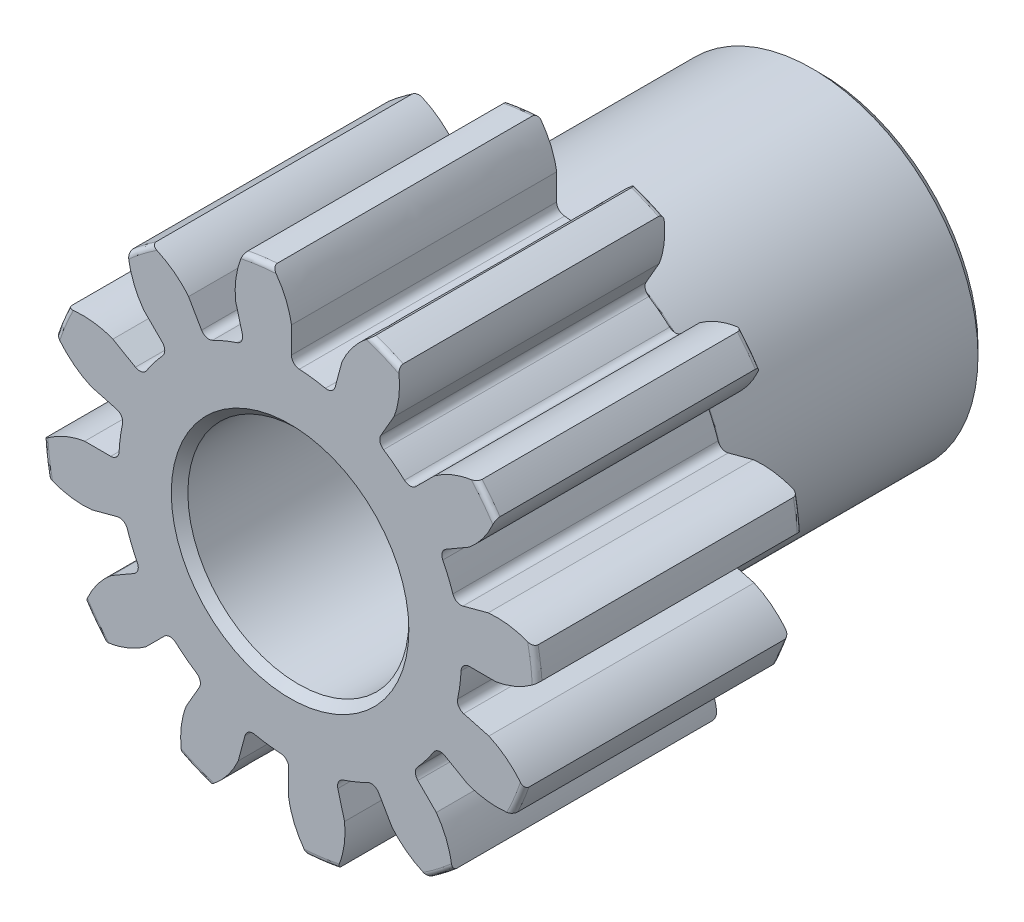
SolidWorks part; units mm, degrees
material "Brass"
ref_plane "Front" through (0, 0, 0) normal (0, 0, 1) x (1, 0, 0)
ref_plane "Top" through (0, 0, 0) normal (0, 1, 0) x (1, 0, 0)
ref_plane "Right" through (0, 0, 0) normal (1, 0, 0) x (0, 0, -1)
sketch "Sketch1" plane through (0, 0, 0) normal (0, 0, 1) x (1, 0, 0)
  line L0 (-152.4, 0) -> (152.4, 0) construction
  circle A0 centre (0, 0) radius 8.89
  circle A1 centre (0, 0) radius 7.62 construction
  circle A3 centre (0, 0) radius 6.1506 construction
  dimension "D1" = 1.4694
  dimension "D2" = 2.7394
  dimension "D3" = 1.27
extrude "Boss-Extrude1" add sketch "Sketch1" against normal blind 9.525
sketch "Sketch2" plane through (0, 0, 0) normal (1, 0, 0) x (0, 0, -1)
  line L0 (9.525, 0) -> (19.05, 0)
  line L1 (9.525, 0) -> (9.525, 5.9531)
  line L2 (9.525, 5.9531) -> (19.05, 5.9531)
  line L3 (19.05, 5.9531) -> (19.05, 0)
  point P5 (19.05, -5.9531)
  point P6 (0, -8.89)
  point P7 (9.525, -8.89)
  point P9 (0, 8.89)
revolve "Revolve1" add sketch "Sketch2" angle 360 mid plane about L0
fillet "Fillet2" radius 0.1778 3 edges at (8.89, 0, -9.525) (8.89, 0, 0) (5.9531, 0, -9.525)
sketch "Sketch3" plane through (0, 0, 0) normal (0, 0, 1) x (1, 0, 0)
  line L0 (0, 0) -> (0, 8.89) construction
  line L1 (-1.8471, 7.1423) -> (0, 7.62)
  line L2 (-9.5921, 7.62) -> (9.5921, 7.62) construction
  line L3 (-9.2865, 5.2183) -> (9.2865, 10.0217) construction
  line L4 (-1.8471, 7.1423) -> (0, 0) construction
  line L5 (-4.563, 5.7968) -> (0, 0) construction
  line L6 (-4.563, 5.7968) -> (-0.6452, 8.8807) construction
  line L7 (-1.288, 7.264) -> (0, 0) construction
  line L8 (-1.288, 7.264) -> (0.027, 7.4971) construction
  arc A0 (-1.8471, 7.1423) -> (-4.563, 5.7968) centre (0, 0) ccw
  circle A1 centre (0, 0) radius 7.62 construction
  circle A2 centre (0, 0) radius 7.3773 construction
  arc A3 (-1.8471, 7.1423) -> (-1.288, 7.264) centre (0, 0) cw
  circle A4 centre (0, 0) radius 8.89 construction
  point P6 (0, 7.62)
  dimension "D1" = 1.9079
  dimension "D3" = 4.9859
  dimension "D5" = 1.3355
  dimension "D2" = 3.0526
  dimension "D4" = 0.5724
sketch "Sketch4" plane through (0, 0, 0) normal (0, 0, 1) x (1, 0, 0)
  line L0 (0, 0) -> (0.9861, 7.4902) construction
  line L1 (0.0483, 7.3771) -> (0.0483, 6.1504)
  line L2 (0, 7.62) -> (1.9722, 7.3604) construction
  line L3 (1.8627, 7.1383) -> (1.5452, 5.9534)
  line L4 (0.0483, 6.1504) -> (0, 0) construction
  line L5 (0, 0) -> (0, 8.89) construction
  line L6 (-4.563, 5.7968) -> (-0.6452, 8.8807) construction
  line L7 (-4.563, 5.7968) -> (-0.6452, 8.8807) construction
  arc A0 (1.5452, 5.9534) -> (0.0483, 6.1504) centre (0, 0) ccw
  arc A1 (0, 7.62) -> (1.9722, 7.3604) centre (0, 0) cw construction
  circle A2 centre (0, 0) radius 7.62 construction
  circle A3 centre (0, 0) radius 7.3773 construction
  circle A4 centre (0, 0) radius 6.1506 construction
  arc A5 (2.9218, 8.4111) -> (-0.6452, 8.8807) centre (0, 0) ccw
  spline S0 degree 2 poles (-0.6452, 8.8807) (-0.0806, 8.1997) (0.0483, 7.3771) knots 0 0 0 1 1 1
  spline S1 degree 2 poles (2.9218, 8.4111) (2.2001, 7.8994) (1.8627, 7.1383) knots 0 0 0 1 1 1
  dimension "D1" = 1.9949
extrude "Cut-Extrude1" cut sketch "Sketch4" against normal through all
fillet "Fillet1" radius 0.2992 2 edges at (1.5452, 5.9534, -4.7625) (0.0483, 6.1504, -4.7625)
pattern_circular "CirPattern1" count 12 over 360 about axis through (0, 0, -9.525) along (0, 0, 1) of "Cut-Extrude1", "Fillet1"
sketch "Sketch5" plane through (0, 0, 0) normal (0, 0, 1) x (1, 0, 0)
  circle A0 centre (0, 0) radius 3.9688
  circle A1 centre (0, 0) radius 3.9688 construction
  dimension "Bore Min" = 7.9375
  dimension "Bore Max" = 7.9375
extrude "Cut-Extrude2" cut sketch "Sketch5" against normal through all
chamfer "Chamfer1" distance 0.2977 angle 45 3 edges at (5.9531, 0, -19.05) (3.9688, 0, 0) (3.9688, 0, -19.05)
sketch "Pitch Dia" plane through (0, 0, 0) normal (0, 0, 1) x (1, 0, 0)
  circle A0 centre (0, 0) radius 7.62 construction
  circle A1 centre (0, 0) radius 7.62
equation "\"D1@Boss-Extrude1\" = \"Face Wd@Sketch2\""
equation "\"D2@Sketch3\" = \"D1@Sketch3\"*1.6"
equation "\"D3@Sketch3\" = \"D1@Sketch3\"+\"D2@Sketch3\"+.001"
equation "\"D4@Sketch3\" = \"D1@Sketch3\"*.3"
equation "\"D5@Sketch3\" = \"D1@Sketch3\"-\"D4@Sketch3\""
equation "\"D1@Sketch4\" = 1.5708/(\"Number of Teeth@Sketch1\"/\"Ptich Dia@Sketch1\")"
equation "\"D1@Chamfer1\" = \"B Hub Dia@Sketch2\"*.025"
equation "\"D1@CirPattern1\" = \"Number of Teeth@Sketch1\""
equation "\"D1@Fillet1\" = \"D1@Sketch4\"*.15"
equation "\"D1@Fillet2\" = \"OD@Sketch1\"*.01"
equation "\"D1@Sketch1\" = 1.157/(\"Number of Teeth@Sketch1\"/\"Ptich Dia@Sketch1\")"
